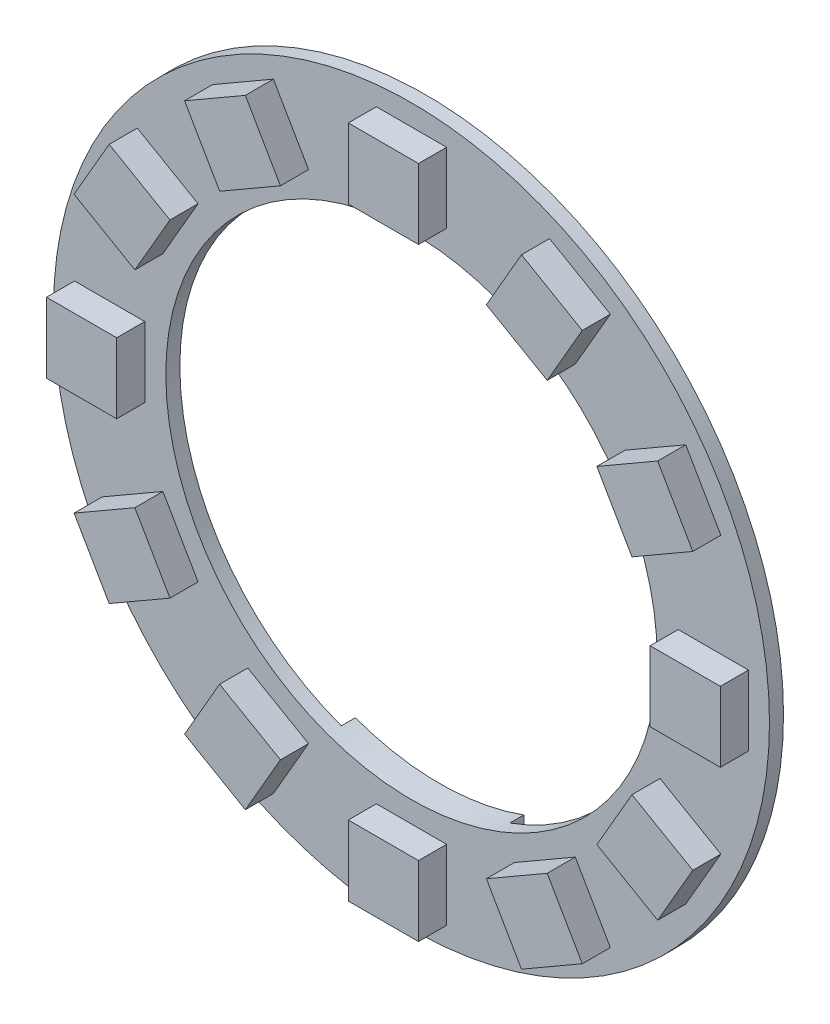
SolidWorks part; units mm, degrees
material "S235JR"
ref_plane "Vorderansicht (XY)" through (0, 0, 0) normal (0, 0, 1) x (1, 0, 0)
ref_plane "Draufansicht (XZ)" through (0, 0, 0) normal (0, 1, 0) x (1, 0, 0)
ref_plane "Seitenansicht (ZY)" through (0, 0, 0) normal (1, 0, 0) x (0, 0, -1)
sketch "Skizze1" plane through (0, 0, 0) normal (0, 0, 1) x (1, 0, 0)
  circle A0 centre (0, 0) radius 17.5
  circle A1 centre (0, 0) radius 25.5
  dimension "D1" = 35
  dimension "D2" = 8
extrude "Aufsatz-Linear austragen1" add sketch "Skizze1" along normal blind 1
sketch "Skizze2" plane through (0, 0, 0) normal (0, 0, -1) x (-1, 0, 0)
  line L0 (-6, -16.4393) -> (-6, -24.7841)
  line L1 (0, -25.5) -> (0, -22.4928) construction
  line L2 (6, -16.4393) -> (6, -24.7841)
  circle A0 centre (0, 0) radius 17.5 construction
  circle A1 centre (0, 0) radius 25.5 construction
  arc A2 (-6, -16.4393) -> (6, -16.4393) centre (0, 0) ccw
  circle A3 centre (0, 0) radius 25.5
  arc A4 (-6, -24.7841) -> (6, -24.7841) centre (0, 0) ccw
  dimension "D1" = 12
  dimension "D2" = 0
extrude "Aufsatz-Linear austragen2" add sketch "Skizze2" along normal blind 1
sketch "Skizze3" plane through (0, 0, 1) normal (0, 0, 1) x (1, 0, 0)
  line L0 (0, -17.5) -> (0, -25.5) construction
  line L1 (-11.6651, -15.2045) -> (-14.1651, -19.5346)
  line L2 (-2.5, -19) -> (2.5, -19)
  line L3 (-2.5, -19) -> (-2.5, -24)
  line L4 (-2.5, -24) -> (2.5, -24)
  line L5 (2.5, -19) -> (2.5, -24)
  line L6 (-2.5, -19) -> (2.5, -24) construction
  line L7 (-2.5, -24) -> (2.5, -19) construction
  line L8 (-11.6651, -15.2045) -> (-7.3349, -17.7045)
  line L9 (-7.3349, -17.7045) -> (-9.8349, -22.0346)
  line L10 (-14.1651, -19.5346) -> (-9.8349, -22.0346)
  line L11 (-17.7045, -7.3349) -> (-22.0346, -9.8349)
  line L12 (-17.7045, -7.3349) -> (-15.2045, -11.6651)
  line L13 (-15.2045, -11.6651) -> (-19.5346, -14.1651)
  line L14 (-22.0346, -9.8349) -> (-19.5346, -14.1651)
  line L15 (-19, 2.5) -> (-24, 2.5)
  line L16 (-19, 2.5) -> (-19, -2.5)
  line L17 (-19, -2.5) -> (-24, -2.5)
  line L18 (-24, 2.5) -> (-24, -2.5)
  line L19 (-15.2045, 11.6651) -> (-19.5346, 14.1651)
  line L20 (-15.2045, 11.6651) -> (-17.7045, 7.3349)
  line L21 (-17.7045, 7.3349) -> (-22.0346, 9.8349)
  line L22 (-19.5346, 14.1651) -> (-22.0346, 9.8349)
  line L23 (-7.3349, 17.7045) -> (-9.8349, 22.0346)
  line L24 (-7.3349, 17.7045) -> (-11.6651, 15.2045)
  line L25 (-11.6651, 15.2045) -> (-14.1651, 19.5346)
  line L26 (-9.8349, 22.0346) -> (-14.1651, 19.5346)
  line L27 (2.5, 19) -> (2.5, 24)
  line L28 (2.5, 19) -> (-2.5, 19)
  line L29 (-2.5, 19) -> (-2.5, 24)
  line L30 (2.5, 24) -> (-2.5, 24)
  line L31 (11.6651, 15.2045) -> (14.1651, 19.5346)
  line L32 (11.6651, 15.2045) -> (7.3349, 17.7045)
  line L33 (7.3349, 17.7045) -> (9.8349, 22.0346)
  line L34 (14.1651, 19.5346) -> (9.8349, 22.0346)
  line L35 (17.7045, 7.3349) -> (22.0346, 9.8349)
  line L36 (17.7045, 7.3349) -> (15.2045, 11.6651)
  line L37 (15.2045, 11.6651) -> (19.5346, 14.1651)
  line L38 (22.0346, 9.8349) -> (19.5346, 14.1651)
  line L39 (19, -2.5) -> (24, -2.5)
  line L40 (19, -2.5) -> (19, 2.5)
  line L41 (19, 2.5) -> (24, 2.5)
  line L42 (24, -2.5) -> (24, 2.5)
  line L43 (15.2045, -11.6651) -> (19.5346, -14.1651)
  line L44 (15.2045, -11.6651) -> (17.7045, -7.3349)
  line L45 (17.7045, -7.3349) -> (22.0346, -9.8349)
  line L46 (19.5346, -14.1651) -> (22.0346, -9.8349)
  line L47 (7.3349, -17.7045) -> (9.8349, -22.0346)
  line L48 (7.3349, -17.7045) -> (11.6651, -15.2045)
  line L49 (11.6651, -15.2045) -> (14.1651, -19.5346)
  line L50 (9.8349, -22.0346) -> (14.1651, -19.5346)
  circle A0 centre (0, 0) radius 17.5 construction
  circle A1 centre (0, 0) radius 25.5 construction
  point P7 (0, -21.5)
  point P58 (0, 0)
  dimension "D1" = 5
  dimension "D2" = 5
  dimension "D3" = 12
extrude "Aufsatz-Linear austragen3" add sketch "Skizze3" along normal blind 2
